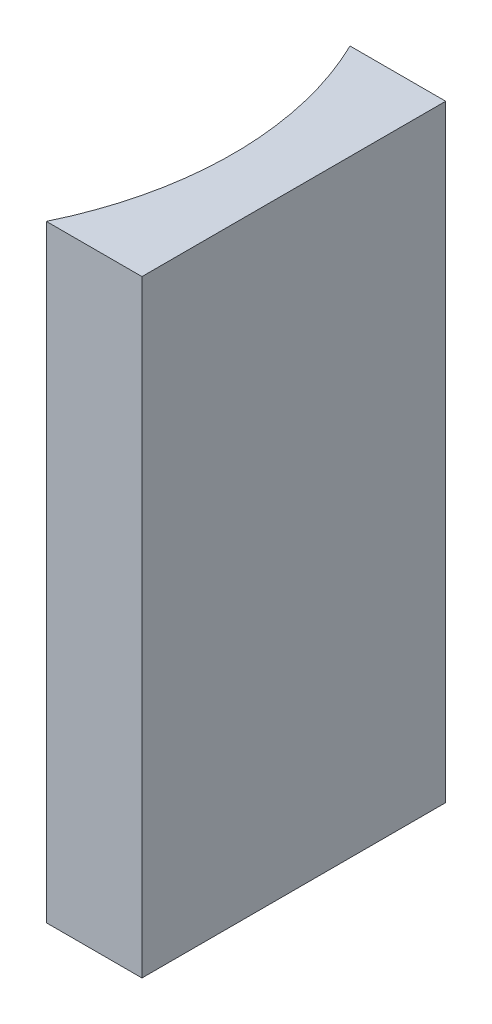
SolidWorks part; units mm, degrees
ref_plane "前视基准面" through (0, 0, 0) normal (0, 0, 1) x (1, 0, 0)
ref_plane "上视基准面" through (0, 0, 0) normal (0, 1, 0) x (1, 0, 0)
ref_plane "右视基准面" through (0, 0, 0) normal (1, 0, 0) x (0, 0, -1)
sketch "草图1" plane through (0, 0, 0) normal (0, 1, 0) x (1, 0, 0)
  line L0 (0, 0) -> (0, -10)
  line L1 (0, 0) -> (-3.1494, 0)
  line L2 (0, -10) -> (-3.1494, -10)
  line L3 (21.2259, -5) -> (-21.2259, -5) construction
  arc A0 (-3.1494, -10) -> (-3.1494, 0) centre (-13.45, -5) ccw
  point P7 (-2, -5)
  point P8 (0, -5)
  dimension "D2" = 11.45
  dimension "D3" = 2
  dimension "D1" = 10
extrude "凸台-拉伸1" add sketch "草图1" along normal blind 20
